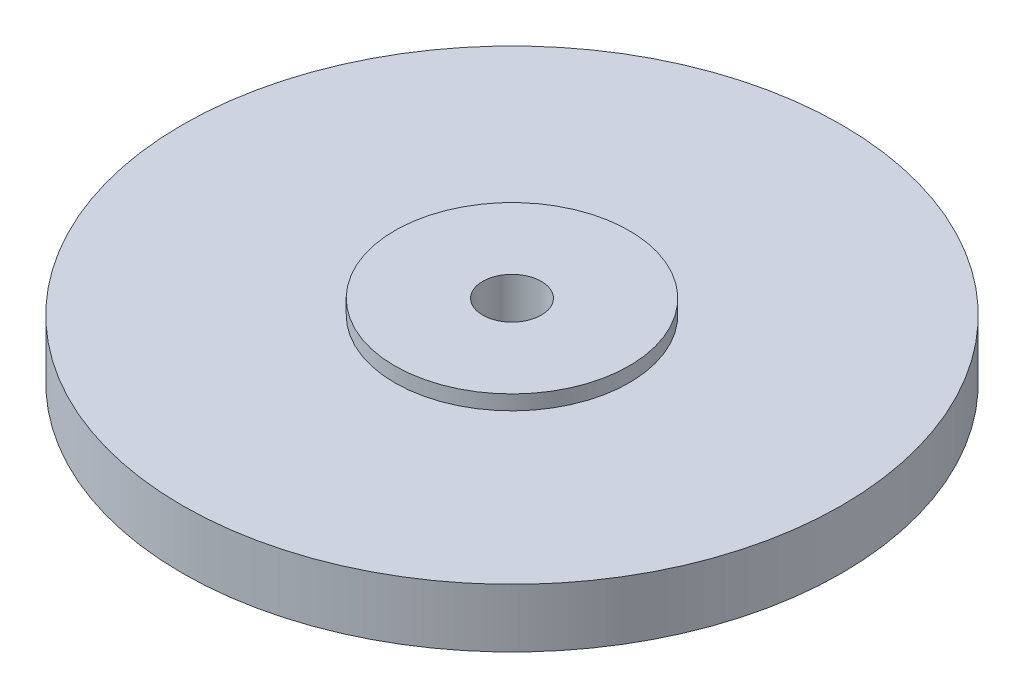
SolidWorks part; units mm, degrees
ref_plane "Plan de face" through (0, 0, 0) normal (0, 0, 1) x (1, 0, 0)
ref_plane "Plan de dessus" through (0, 0, 0) normal (0, 1, 0) x (1, 0, 0)
ref_plane "Plan de droite" through (0, 0, 0) normal (1, 0, 0) x (0, 0, -1)
sketch "Esquisse1" plane through (0, 0, 0) normal (0, 0, 1) x (1, 0, 0)
  line L0 (0, 8.6266) -> (0, -8.6266) construction
  line L1 (2, 3) -> (2, -13)
  line L2 (2, -13) -> (4, -13)
  line L3 (4, -13) -> (4, -2)
  line L4 (8, 2) -> (8, 3)
  line L5 (8, 3) -> (2, 3)
  line L6 (4, -2) -> (22.5, -2)
  line L7 (22.5, -2) -> (22.5, 2)
  line L12 (22.5, 2) -> (8, 2)
  line L13 (0, 0) -> (37.2784, 0) construction
  dimension "D1" = 4
  dimension "D2" = 45
  dimension "D3" = 4
  dimension "D4" = 8
  dimension "D5" = 16
  dimension "D6" = 1
  dimension "D7" = 16
revolve "Révolution1" add sketch "Esquisse1" angle 360 about L0
